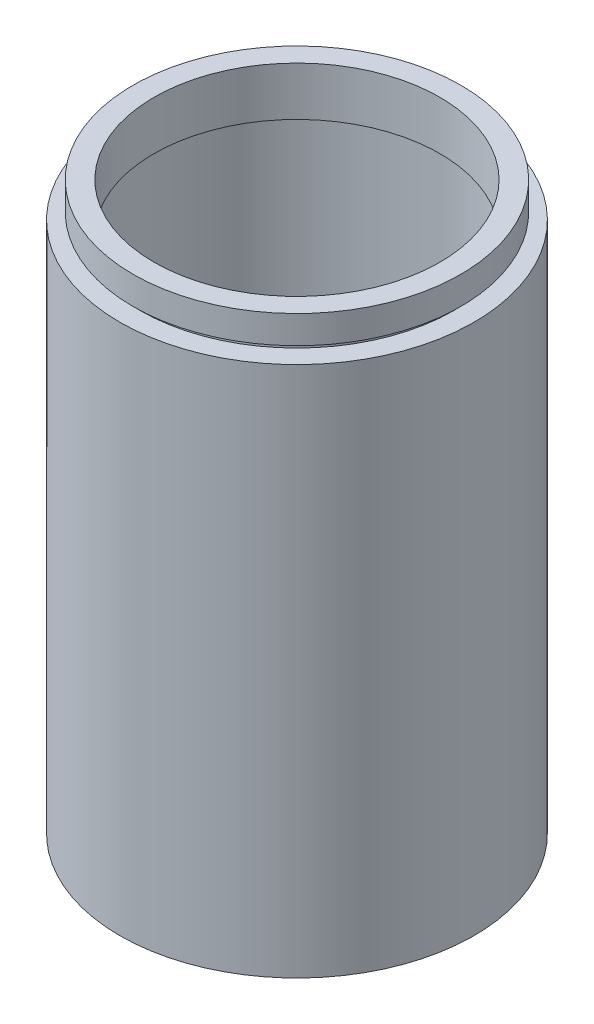
SolidWorks part; units mm, degrees
ref_plane "前视基准面" through (0, 0, 0) normal (0, 0, 1) x (1, 0, 0)
ref_plane "上视基准面" through (0, 0, 0) normal (0, 1, 0) x (1, 0, 0)
ref_plane "右视基准面" through (0, 0, 0) normal (1, 0, 0) x (0, 0, -1)
sketch "草图1" plane through (0, 0, 0) normal (0, 0, 1) x (1, 0, 0)
  line L0 (0, 161.3762) -> (0, 0) construction
  line L1 (141.7365, 0) -> (-131.7984, 0) construction
  line L2 (22.5, 73.2) -> (23.5, 73.2)
  line L3 (23.5, 73.2) -> (23.5, 74.2)
  line L4 (23.5, 74.2) -> (20.5, 74.2)
  line L5 (20.5, 74.2) -> (20.5, 81.2)
  line L6 (23.5, 77.2) -> (23.5, 81.2)
  line L7 (25.4, 76.2) -> (25.4, 0)
  line L8 (25.4, 0) -> (22.5, 0)
  line L9 (22.5, 0) -> (22.5, 5.5)
  line L10 (25.4, 76.2) -> (23.5, 76.2)
  line L11 (20.5, 81.2) -> (23.5, 81.2)
  line L12 (23.5, 77.2) -> (22.5, 77.2)
  line L13 (22.5, 77.2) -> (22.5, 76.2)
  line L14 (22.5, 6.5) -> (22.5, 73.2)
  line L15 (22.5, 5.5) -> (23.5, 5.5)
  line L16 (23.5, 5.5) -> (23.5, 6.5)
  line L17 (23.5, 6.5) -> (22.5, 6.5)
  line L18 (22.5, 76.2) -> (23.5, 76.2)
  point P10 (24.45, 76.2)
  point P24 (23.481, 76.2)
  dimension "D2" = 76.2
  dimension "D3" = 1
  dimension "D4" = 5.5
  dimension "D5" = 20.5
  dimension "D6" = 23.5
  dimension "D7" = 22.5
  dimension "D8" = 1
  dimension "D9" = 7
  dimension "D10" = 5
  dimension "D11" = 25.4
  dimension "D12" = 23.5
  dimension "D13" = 1
revolve "旋转1" add sketch "草图1" angle 360 about L0
cosmetic thread "装饰螺纹线1"
cosmetic thread "装饰螺纹线2"
cosmetic thread "装饰螺纹线3"
cosmetic thread "装饰螺纹线4"
